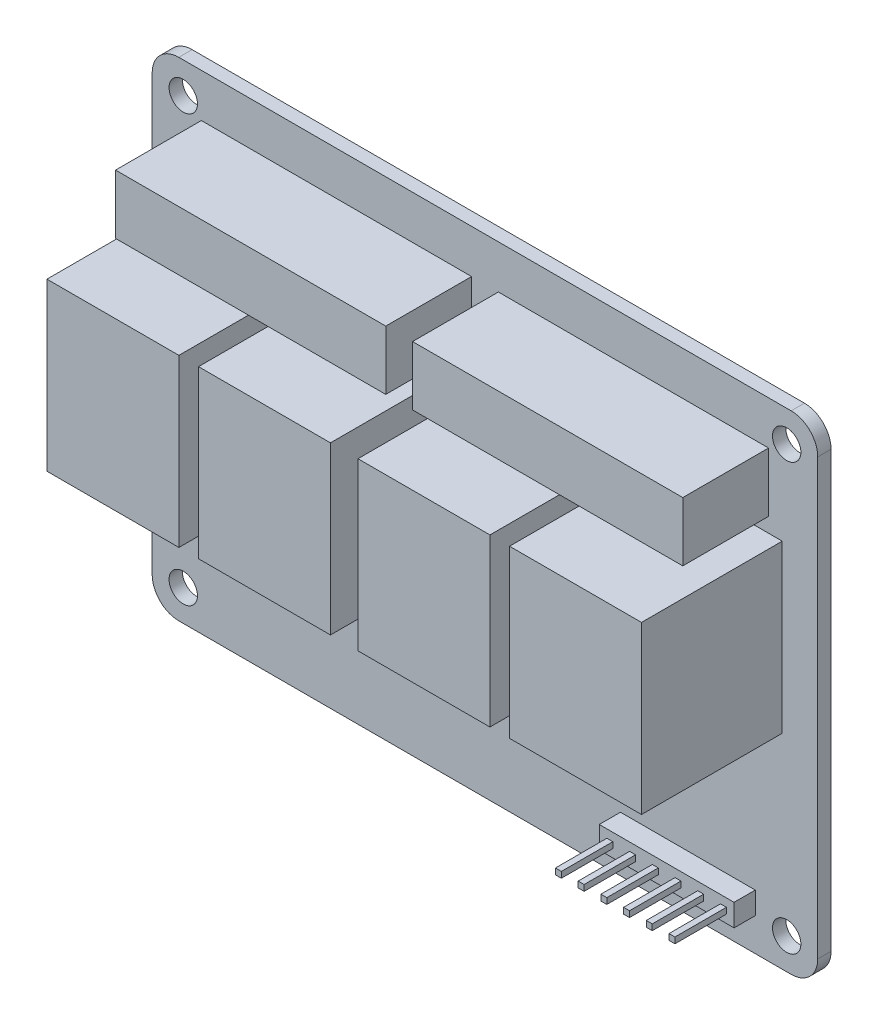
SolidWorks part; units mm, degrees
ref_plane "Alzado" through (0, 0, 0) normal (0, 0, 1) x (1, 0, 0)
ref_plane "Planta" through (0, 0, 0) normal (0, 1, 0) x (1, 0, 0)
ref_plane "Vista lateral" through (0, 0, 0) normal (1, 0, 0) x (0, 0, -1)
sketch "Croquis1" plane through (0, 0, 0) normal (0, 0, 1) x (1, 0, 0)
  line L1 (-37.5, 27.5) -> (37.5, 27.5)
  line L2 (-37.5, 27.5) -> (-37.5, -27.5)
  line L3 (-37.5, -27.5) -> (37.5, -27.5)
  line L4 (37.5, 27.5) -> (37.5, -27.5)
  point P4 (0, 27.5)
  point P6 (-37.5, 0)
  dimension "D1" = 75
  dimension "D2" = 55
extrude "Saliente-Extruir1" add sketch "Croquis1" along normal blind 1.5
fillet "Redondeo1" radius 3 4 edges at (-37.5, -27.5, 0.75) (37.5, -27.5, 0.75) (-37.5, 27.5, 0.75) (37.5, 27.5, 0.75)
hole_wizard "Taladro de margen para M31" positions "Croquis3" profile "Croquis2" hole size "M3" standard "Ansi Metric" end condition through all
sketch "Croquis3" plane through (0, 0, 1.5) normal (0, 0, 1) x (1, 0, 0)
  line L0 (-37.5, 24.5) -> (-37.5, -24.5) construction
  line L1 (34.5, 27.5) -> (-34.5, 27.5) construction
  line L2 (-34.5, -27.5) -> (34.5, -27.5) construction
  line L3 (37.5, -24.5) -> (37.5, 24.5) construction
  point P0 (-34, 24)
  point P2 (-34, -24)
  point P4 (34, 24)
  point P6 (34, -24)
  dimension "D1" = 3.5
  dimension "D2" = 3.5
  dimension "D3" = 3.5
  dimension "D4" = 3.5
sketch "Croquis2" plane through (-34, 24, 1.5) normal (1, 0, 0) x (0, -1, 0)
  line L0 (0, 0) -> (0, 1.5)
  line L1 (0, 1.5) -> (1.6, 1.5)
  line L2 (1.6, 1.5) -> (1.6, 0)
  line L5 (1.6, 0) -> (0, 0)
  line L11 (0, -6.35) -> (0, 107.95) construction
  dimension "Diámetro de taladro hasta el siguiente" = 3.2
  dimension "Profundidad de taladro hasta el siguiente" = 1.5
sketch "Croquis4" plane through (0, 0, 1.5) normal (0, 0, 1) x (1, 0, 0)
  line L0 (-37.5, 24.5) -> (-37.5, -24.5) construction
  line L1 (-33.5, 14.28) -> (-18.63, 14.28)
  line L2 (-33.5, 14.28) -> (-33.5, -4.47)
  line L3 (-33.5, -4.47) -> (-18.63, -4.47)
  line L4 (-18.63, 14.28) -> (-18.63, -4.47)
  line L5 (-16.42, 14.28) -> (-1.55, 14.28)
  line L6 (-16.42, 14.28) -> (-16.42, -4.47)
  line L7 (-16.42, -4.47) -> (-1.55, -4.47)
  line L8 (-1.55, 14.28) -> (-1.55, -4.47)
  line L9 (34.5, 27.5) -> (-34.5, 27.5) construction
  line L11 (0, 0) -> (0, 27.5) construction
  line L12 (1.55, 14.28) -> (1.55, -4.47)
  line L13 (16.42, -4.47) -> (1.55, -4.47)
  line L14 (16.42, 14.28) -> (16.42, -4.47)
  line L15 (16.42, 14.28) -> (1.55, 14.28)
  line L16 (18.63, 14.28) -> (18.63, -4.47)
  line L17 (33.5, -4.47) -> (18.63, -4.47)
  line L18 (33.5, 14.28) -> (33.5, -4.47)
  line L19 (33.5, 14.28) -> (18.63, 14.28)
  dimension "D1" = 14.87
  dimension "D2" = 18.75
  dimension "D3" = 2.21
  dimension "D4" = 4
  dimension "D5" = 13.22
extrude "Saliente-Extruir2" add sketch "Croquis4" along normal blind 15.86
sketch "Croquis5" plane through (0, 0, 1.5) normal (0, 0, 1) x (1, 0, 0)
  line L0 (34.5, 27.5) -> (-34.5, 27.5) construction
  line L1 (-31.96, 22.6) -> (-1.51, 22.6)
  line L2 (-31.96, 22.6) -> (-31.96, 15.93)
  line L3 (-31.96, 15.93) -> (-1.51, 15.93)
  line L4 (-1.51, 22.6) -> (-1.51, 15.93)
  line L5 (-34.5, -27.5) -> (34.5, -27.5) construction
  line L6 (-37.5, 24.5) -> (-37.5, -24.5) construction
  line L7 (0, 0) -> (0, 27.5) construction
  line L8 (1.51, 22.6) -> (1.51, 15.93)
  line L9 (31.96, 15.93) -> (1.51, 15.93)
  line L10 (31.96, 22.6) -> (31.96, 15.93)
  line L11 (31.96, 22.6) -> (1.51, 22.6)
  dimension "D1" = 30.45
  dimension "D2" = 4.9
  dimension "D3" = 43.43
  dimension "D4" = 5.54
extrude "Saliente-Extruir3" add sketch "Croquis5" along normal blind 9.67
sketch "Croquis6" plane through (0, 0, 1.5) normal (0, 0, 1) x (1, 0, 0)
  line L0 (-34.5, -27.5) -> (34.5, -27.5) construction
  line L1 (15.27, -21.29) -> (30.46, -21.29)
  line L2 (15.27, -21.29) -> (15.27, -23.79)
  line L3 (15.27, -23.79) -> (30.46, -23.79)
  line L4 (30.46, -21.29) -> (30.46, -23.79)
  line L5 (37.5, -24.5) -> (37.5, 24.5) construction
  dimension "D1" = 3.71
  dimension "D2" = 7.04
  dimension "D3" = 15.19
  dimension "D4" = 2.5
extrude "Saliente-Extruir4" add sketch "Croquis6" along normal blind 2.39
sketch "Croquis7" plane through (0, 0, 3.89) normal (0, 0, 1) x (1, 0, 0)
  line L0 (15.27, -21.29) -> (15.27, -23.79) construction
  line L1 (16.13, -22.205) -> (16.8, -22.205)
  line L2 (16.13, -22.205) -> (16.13, -22.875)
  line L3 (16.13, -22.875) -> (16.8, -22.875)
  line L4 (16.8, -22.205) -> (16.8, -22.875)
  line L5 (18.69, -22.205) -> (19.36, -22.205)
  line L6 (18.69, -22.205) -> (18.69, -22.875)
  line L7 (18.69, -22.875) -> (19.36, -22.875)
  line L8 (19.36, -22.205) -> (19.36, -22.875)
  line L9 (21.25, -22.205) -> (21.92, -22.205)
  line L10 (21.25, -22.205) -> (21.25, -22.875)
  line L11 (21.25, -22.875) -> (21.92, -22.875)
  line L12 (21.92, -22.205) -> (21.92, -22.875)
  line L13 (15.27, -22.54) -> (16.13, -22.54) construction
  line L14 (22.865, -21.29) -> (22.865, -23.79) construction
  line L15 (30.46, -21.29) -> (15.27, -21.29) construction
  line L16 (15.27, -23.79) -> (30.46, -23.79) construction
  line L17 (23.81, -22.205) -> (23.81, -22.875)
  line L18 (24.48, -22.875) -> (23.81, -22.875)
  line L19 (24.48, -22.205) -> (24.48, -22.875)
  line L20 (24.48, -22.205) -> (23.81, -22.205)
  line L21 (26.37, -22.205) -> (26.37, -22.875)
  line L22 (27.04, -22.875) -> (26.37, -22.875)
  line L23 (27.04, -22.205) -> (27.04, -22.875)
  line L24 (27.04, -22.205) -> (26.37, -22.205)
  line L25 (28.93, -22.205) -> (28.93, -22.875)
  line L26 (29.6, -22.875) -> (28.93, -22.875)
  line L27 (29.6, -22.205) -> (29.6, -22.875)
  line L28 (29.6, -22.205) -> (28.93, -22.205)
  dimension "D1" = 0.67
  dimension "D2" = 1.89
  dimension "D3" = 0.945
  dimension "D4" = 1.89
extrude "Saliente-Extruir5" add sketch "Croquis7" along normal blind 5.8
